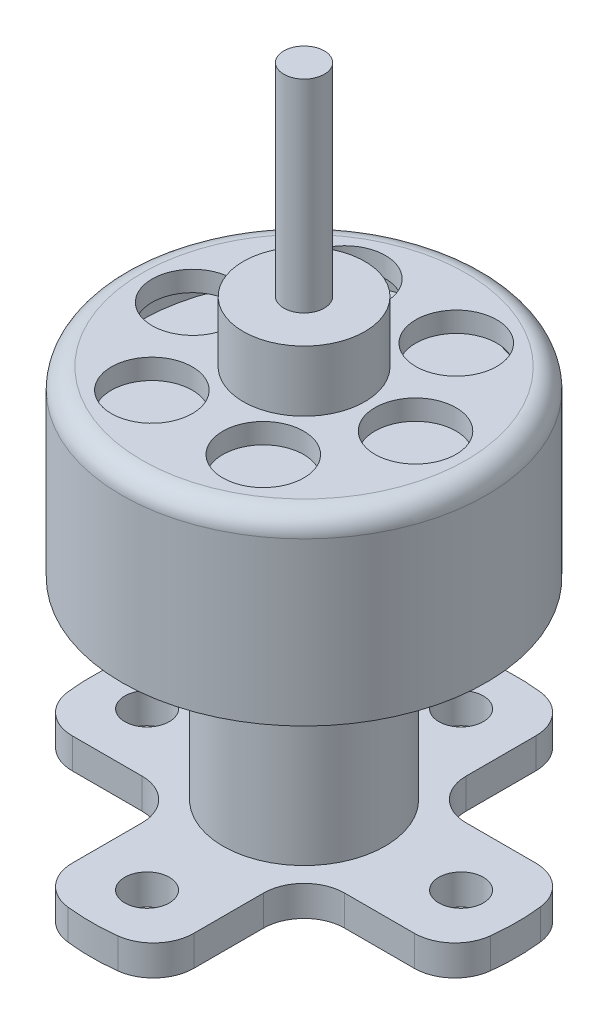
SolidWorks part; units mm, degrees
ref_plane "Front Plane" through (0, 0, 0) normal (0, 0, 1) x (1, 0, 0)
ref_plane "Top Plane" through (0, 0, 0) normal (0, 1, 0) x (1, 0, 0)
ref_plane "Right Plane" through (0, 0, 0) normal (1, 0, 0) x (0, 0, -1)
sketch "Sketch1" plane through (0, 0, 0) normal (0, 1, 0) x (1, 0, 0)
  line L0 (-3, 10.0623) -> (-3, 3)
  line L1 (3, -10.0623) -> (3, -3)
  line L2 (-10.0623, 3) -> (-3, 3)
  line L3 (10.0623, -3) -> (3, -3)
  line L4 (-3, -3) -> (-10.0623, -3)
  line L5 (3, 3) -> (10.0623, 3)
  line L6 (3, 3) -> (3, 10.0623)
  line L7 (-3, -3) -> (-3, -10.0623)
  arc A0 (-10.0623, 3) -> (-10.0623, -3) centre (0, 0) ccw
  arc A1 (-3, -10.0623) -> (3, -10.0623) centre (0, 0) ccw
  arc A2 (10.0623, -3) -> (10.0623, 3) centre (0, 0) ccw
  arc A3 (3, 10.0623) -> (-3, 10.0623) centre (0, 0) ccw
  dimension "D1" = 21
  dimension "D2" = 6
extrude "Boss-Extrude1" add sketch "Sketch1" along normal blind 1.5
sketch "Sketch2" plane through (0, 1.5, 0) normal (0, 1, 0) x (1, 0, 0)
  circle A0 centre (-7.75, 0) radius 1.1
  circle A1 centre (0, 7.75) radius 1.1
  circle A2 centre (7.75, 0) radius 1.1
  circle A3 centre (0, -7.75) radius 1.1
  point P12 (0, 0)
  dimension "D1" = 2.2
  dimension "D2" = 7.75
  dimension "D3" = 4
extrude "Cut-Extrude1" cut sketch "Sketch2" against normal through all
fillet "Fillet1" radius 2 12 edges at (-3, 0.75, 10.0623) (3, 0.75, 10.0623) (10.0623, 0.75, 3) (10.0623, 0.75, -3) (3, 0.75, -10.0623) (-3, 0.75, -10.0623) (-10.0623, 0.75, -3) (-10.0623, 0.75, 3) (3, 0.75, -3) (-3, 0.75, -3) (-3, 0.75, 3) (3, 0.75, 3)
sketch "Sketch3" plane through (0, 1.5, 0) normal (0, 1, 0) x (1, 0, 0)
  circle A0 centre (0, 0) radius 4
  dimension "D1" = 8
extrude "Boss-Extrude2" add sketch "Sketch3" along normal blind 9.5
sketch "Sketch4" plane through (0, 11, 0) normal (0, 1, 0) x (1, 0, 0)
  circle A0 centre (0, 0) radius 9
  dimension "D1" = 18
extrude "Boss-Extrude3" add sketch "Sketch4" along normal blind 9
fillet "Fillet2" radius 1 1 edges at (0, 20, 9)
sketch "Sketch5" plane through (0, 20, 0) normal (0, 1, 0) x (1, 0, 0)
  circle A0 centre (0, 0) radius 3
  dimension "D1" = 6
extrude "Boss-Extrude4" add sketch "Sketch5" along normal blind 3
sketch "Sketch6" plane through (0, 23, 0) normal (0, 1, 0) x (1, 0, 0)
  circle A0 centre (0, 0) radius 1
  dimension "D1" = 2
extrude "Boss-Extrude5" add sketch "Sketch6" along normal blind 10
sketch "Sketch7" plane through (0, 20, 0) normal (0, 1, 0) x (1, 0, 0)
  circle A0 centre (-5.5, 0) radius 2
  circle A1 centre (-2.75, 4.7631) radius 2
  circle A2 centre (2.75, 4.7631) radius 2
  circle A3 centre (5.5, 0) radius 2
  circle A4 centre (2.75, -4.7631) radius 2
  circle A5 centre (-2.75, -4.7631) radius 2
  point P15 (0, 0)
  dimension "D1" = 4
  dimension "D2" = 5.5
  dimension "D3" = 6
extrude "Cut-Extrude2" cut sketch "Sketch7" against normal blind 1
sketch "Sketch8" plane through (0, 19, 0) normal (0, 1, 0) x (1, 0, 0)
  circle A0 centre (0, 0) radius 8
extrude "Cut-Extrude3" cut sketch "Sketch8" against normal blind 1
